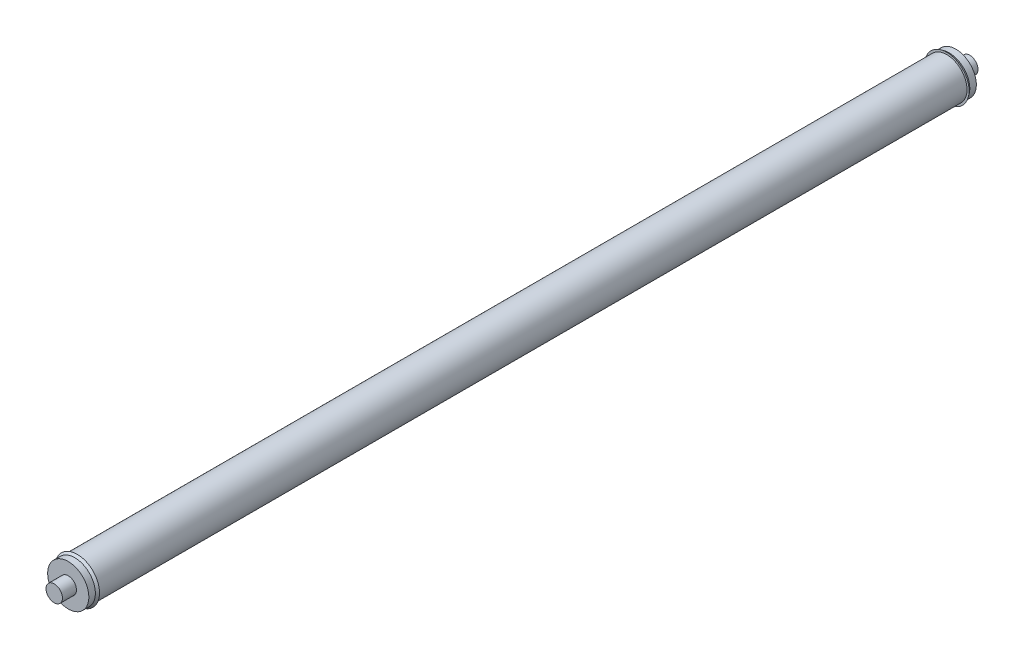
SolidWorks part; units mm, degrees
ref_plane "Front Plane" through (0, 0, 0) normal (0, 0, 1) x (1, 0, 0)
ref_plane "Top Plane" through (0, 0, 0) normal (0, 1, 0) x (1, 0, 0)
ref_plane "Right Plane" through (0, 0, 0) normal (1, 0, 0) x (0, 0, -1)
sketch "Sketch1" plane through (0, 0, 0) normal (0, 1, 0) x (1, 0, 0)
  line L0 (0, 71.4139) -> (0, -79.1646) construction
  line L1 (0, 56.5) -> (0, 54.77)
  line L2 (0, 54.77) -> (0, -54.77)
  line L3 (2.5, -53.66) -> (2.75, -53.66)
  line L5 (1.015, 56.5) -> (0, 56.5)
  line L6 (1.015, 54.77) -> (1.015, 56.5)
  line L7 (2.54, 54.77) -> (1.015, 54.77)
  line L8 (2.75, -53.66) -> (2.54, -53.96)
  line L9 (2.54, -53.96) -> (2.54, -54.77)
  line L10 (2.54, 53.96) -> (2.54, 54.77)
  line L11 (2.54, -54.77) -> (1.015, -54.77)
  line L12 (2.5, 53.66) -> (2.75, 53.66)
  line L13 (1.015, -54.77) -> (1.015, -56.5)
  line L14 (1.015, -56.5) -> (0, -56.5)
  line L15 (0, -56.5) -> (0, -54.77)
  line L16 (-19.6315, 0) -> (30.0358, 0) construction
  line L17 (2.75, 53.66) -> (2.54, 53.96)
  line L18 (2.5, -53.66) -> (2.5, 53.66)
  dimension "D1" = 5.08
  dimension "D2" = 5
  dimension "D3" = 2.03
  dimension "D4" = 113
  dimension "D6" = 0.81
  dimension "D7" = 5.5
  dimension "D8" = 0.3
  dimension "D9" = 1.73
revolve "Revolve1" add sketch "Sketch1" angle 360 about L0
